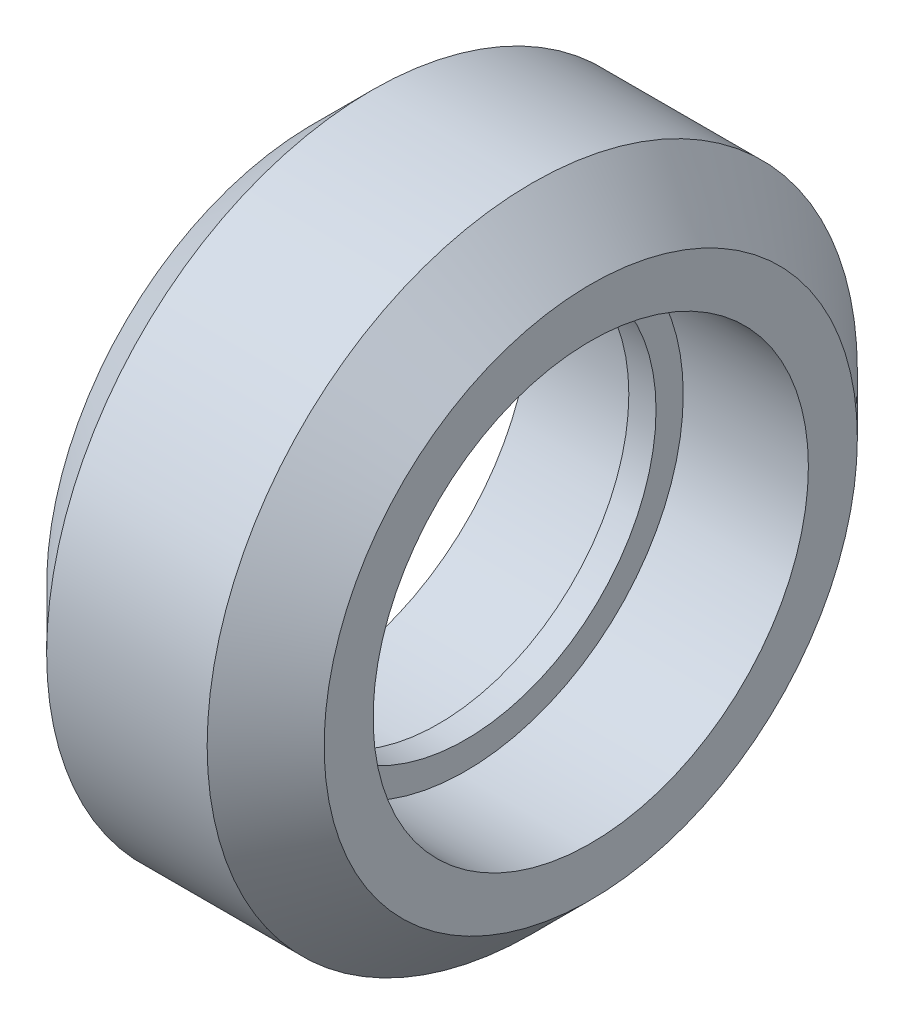
SolidWorks part; units mm, degrees
material "Delrin 2700 NC010, Low Viscosity Acetal Copolymer (SS)"
ref_plane "Front Plane" through (0, 0, 0) normal (0, 0, 1) x (1, 0, 0)
ref_plane "Top Plane" through (0, 0, 0) normal (0, 1, 0) x (1, 0, 0)
ref_plane "Right Plane" through (0, 0, 0) normal (1, 0, 0) x (0, 0, -1)
sketch "Sketch1" plane through (0, 0, 0) normal (0, 0, 1) x (1, 0, 0)
  line L0 (0.5, 7) -> (-0.5, 7)
  line L1 (-0.5, 7) -> (-0.5, 8)
  line L2 (-0.5, 8) -> (-5.1, 8)
  line L3 (-5.1, 8) -> (-5.1, 9.8)
  line L4 (-5.1, 9.8) -> (-2.95, 11.95)
  line L5 (-2.95, 11.95) -> (2.95, 11.95)
  line L6 (0, 11.95) -> (0, 7) construction
  line L7 (5.1, 9.8) -> (2.95, 11.95)
  line L8 (5.1, 8) -> (5.1, 9.8)
  line L9 (0.5, 8) -> (5.1, 8)
  line L10 (0.5, 7) -> (0.5, 8)
  line L11 (0, 0) -> (-12.6359, 0) construction
  dimension "D2" = 16
  dimension "D3" = 23.9
  dimension "D4" = 1
  dimension "D5" = 45
  dimension "D6" = 10.2
  dimension "D7" = 5.9
  dimension "D8" = 14
revolve "Revolve1" add sketch "Sketch1" angle 360 about L11
